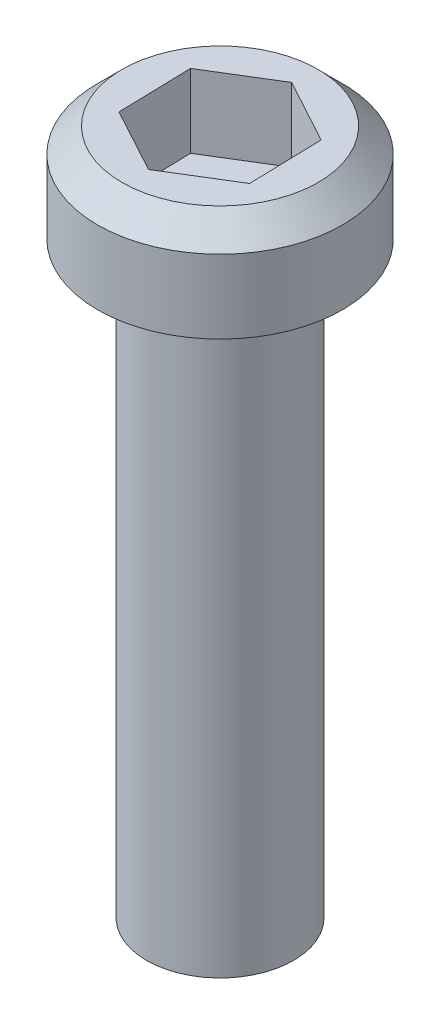
SolidWorks part; units mm, degrees
ref_plane "Front Plane" through (0, 0, 0) normal (0, 0, 1) x (1, 0, 0)
ref_plane "Top Plane" through (0, 0, 0) normal (0, 1, 0) x (1, 0, 0)
ref_plane "Right Plane" through (0, 0, 0) normal (1, 0, 0) x (0, 0, -1)
sketch "Sketch1" plane through (0, 0, 0) normal (0, 1, 0) x (1, 0, 0)
  circle A0 centre (-74.5378, 155.6271) radius 1.5
  dimension "D1" = 3
extrude "Boss-Extrude1" add sketch "Sketch1" against normal blind 12
sketch "Sketch2" plane through (0, 0, 0) normal (0, 1, 0) x (1, 0, 0)
  circle A0 centre (-74.5378, 155.6271) radius 2.5
  dimension "D1" = 5
extrude "Boss-Extrude2" add sketch "Sketch2" along normal blind 2
chamfer "Chamfer1" distance 0.5 angle 45 1 edges at (-74.5378, 2, -153.1271)
sketch "Sketch3" plane through (0, 2, 0) normal (0, 1, 0) x (1, 0, 0)
  line L1 (-73.2197, 154.9112) -> (-73.2588, 156.4107)
  line L2 (-73.2588, 156.4107) -> (-74.5769, 157.1266)
  line L3 (-74.5769, 157.1266) -> (-75.856, 156.343)
  line L4 (-75.856, 156.343) -> (-75.8169, 154.8435)
  line L5 (-75.8169, 154.8435) -> (-74.4987, 154.1276)
  line L6 (-74.4987, 154.1276) -> (-73.2197, 154.9112)
  circle A0 centre (-74.5378, 155.6271) radius 1.299 construction
  dimension "1.5" = 1.5
extrude "Cut-Extrude1" cut sketch "Sketch3" against normal blind 1.5
